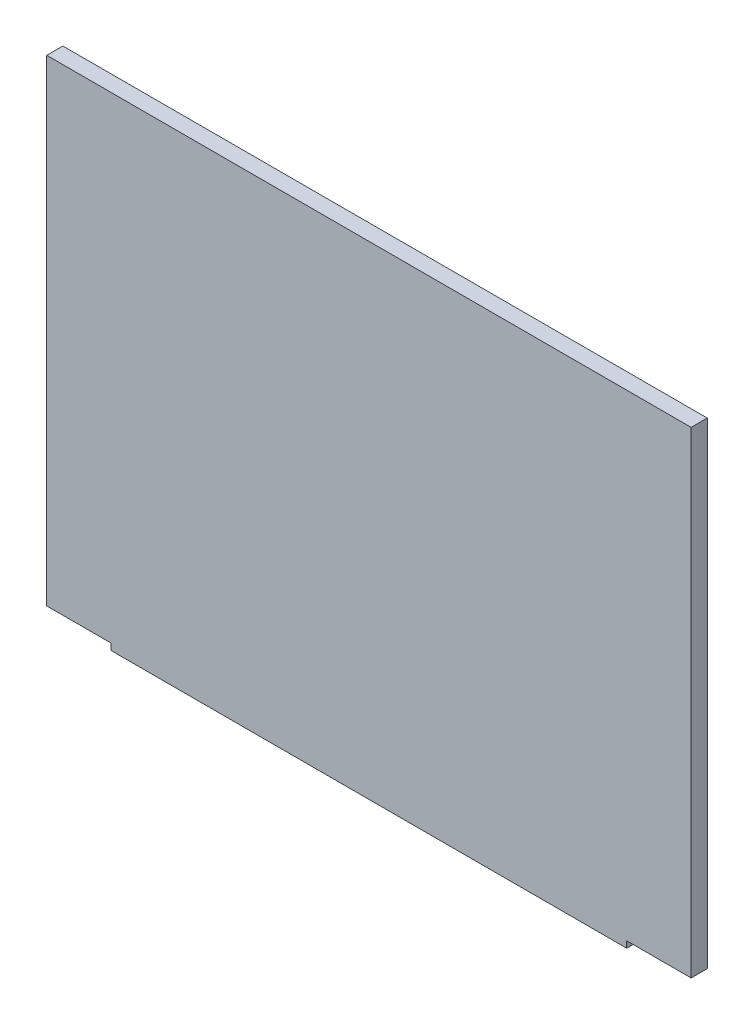
SolidWorks part; units mm, degrees
ref_plane "Plan de face" through (0, 0, 0) normal (0, 0, 1) x (1, 0, 0)
ref_plane "Plan de dessus" through (0, 0, 0) normal (0, 1, 0) x (1, 0, 0)
ref_plane "Plan de droite" through (0, 0, 0) normal (1, 0, 0) x (0, 0, -1)
sketch "Esquisse1" plane through (0, 0, 0) normal (0, 0, 1) x (1, 0, 0)
  line L0 (-11.0385, 6.9811) -> (188.9615, 6.9811)
  line L1 (188.9615, 6.9811) -> (188.9615, -143.0189)
  line L2 (188.9615, -143.0189) -> (-11.0385, -143.0189)
  line L3 (-11.0385, 6.9811) -> (-11.0385, -143.0189)
  dimension "D1" = 200
  dimension "D2" = 150
extrude "Boss.-Extru.1" add sketch "Esquisse1" along normal blind 5
sketch "Esquisse2" plane through (0, 0, 5) normal (0, 0, 1) x (1, 0, 0)
  line L1 (188.9615, -143.0189) -> (168.9615, -143.0189)
  line L2 (188.9615, -143.0189) -> (188.9615, -141.0189)
  line L3 (188.9615, -141.0189) -> (168.9615, -141.0189)
  line L4 (168.9615, -143.0189) -> (168.9615, -141.0189)
  line L5 (-11.0385, -143.0189) -> (8.9615, -143.0189)
  line L6 (-11.0385, -143.0189) -> (-11.0385, -141.0189)
  line L7 (-11.0385, -141.0189) -> (8.9615, -141.0189)
  line L8 (8.9615, -143.0189) -> (8.9615, -141.0189)
  dimension "D1" = 20
  dimension "D2" = 2
  dimension "D3" = 20
  dimension "D4" = 2
extrude "Enlèv. mat.-Extru.1" cut sketch "Esquisse2" against normal blind 10
